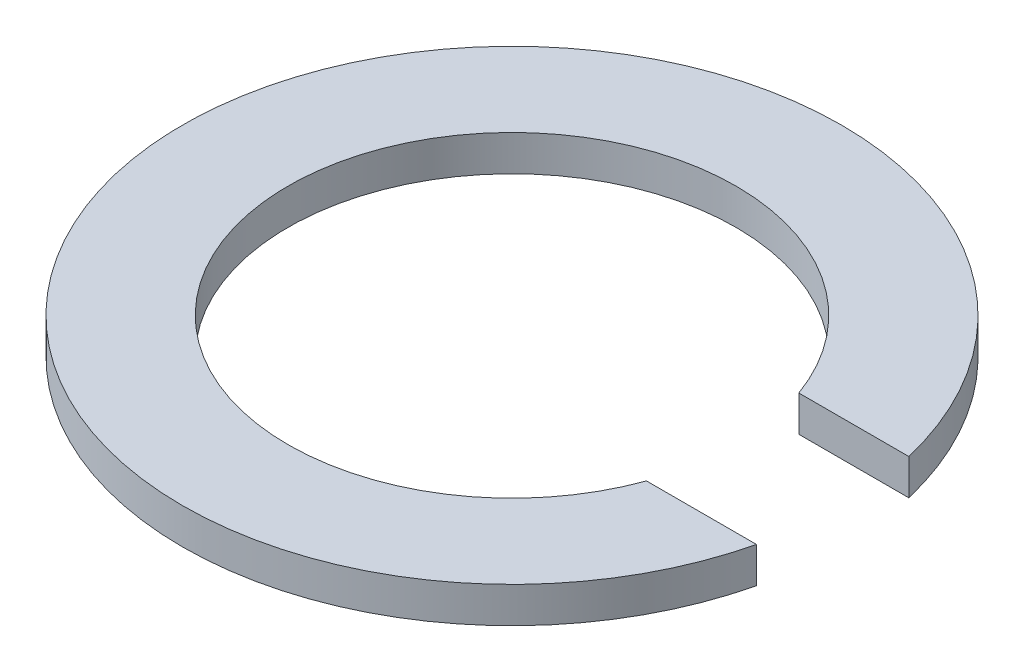
SolidWorks part; units mm, degrees
material "Bismuth"
ref_plane "Front" through (0, 0, 0) normal (0, 0, 1) x (1, 0, 0)
ref_plane "Top" through (0, 0, 0) normal (0, 1, 0) x (1, 0, 0)
ref_plane "Right" through (0, 0, 0) normal (1, 0, 0) x (0, 0, -1)
sketch "Sketch1" plane through (0, 0, 0) normal (0, 1, 0) x (1, 0, 0)
  line L2 (81.8166, -29.5811) -> (124.535, -29.5811)
  line L3 (81.8165, 29.5813) -> (124.5349, 29.5813)
  arc A0 (81.8165, 29.5813) -> (81.8166, -29.5811) centre (0, 0) ccw
  arc A1 (124.5349, 29.5813) -> (124.535, -29.5811) centre (0, 0) ccw
  point P4 (0, 0)
  point P7 (0, 0)
  point P8 (0, 0)
  point P9 (0, 0)
  point P10 (0, 0)
  point P11 (0, 0)
  point P12 (0, 0)
  point P13 (0, 0)
  point P14 (0, 0)
  point P15 (0, 0)
  point P16 (0, 0)
extrude "Boss-Extrude2" add sketch "Sketch1" along normal blind 13.9 separate body contours A0 L2 A1 L3
